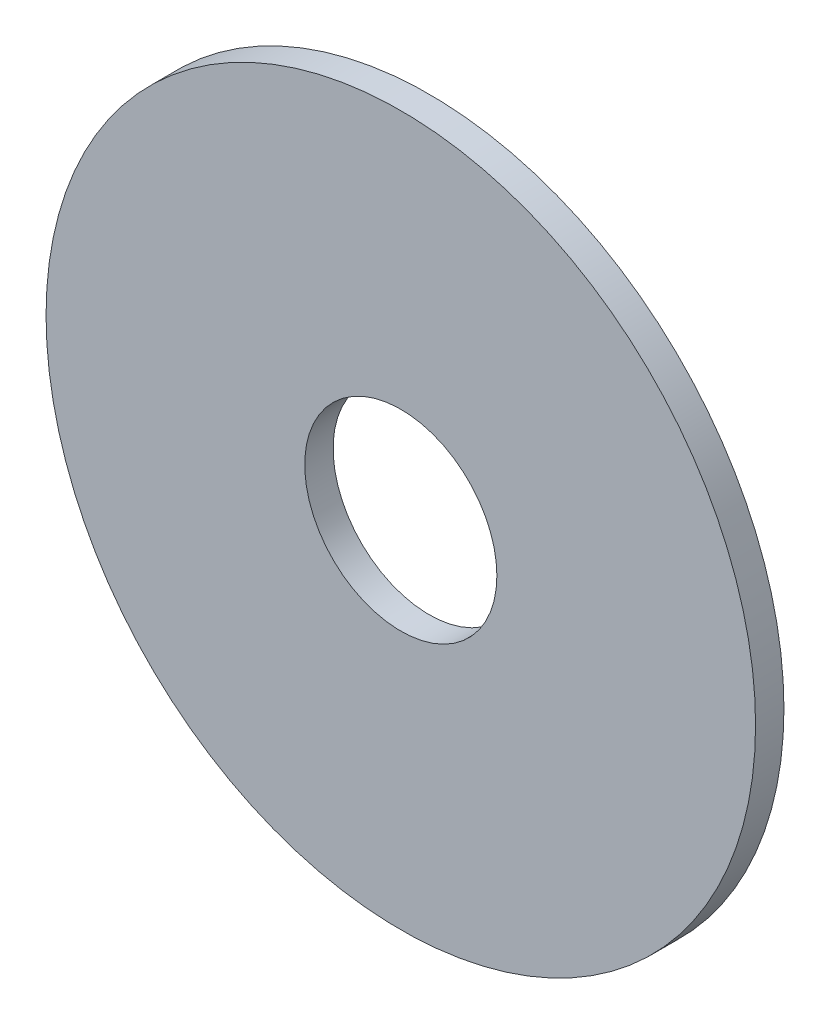
SolidWorks part; units mm, degrees
material "Plain Carbon Steel"
ref_plane "Front Plane" through (0, 0, 0) normal (0, 0, 1) x (1, 0, 0)
ref_plane "Top Plane" through (0, 0, 0) normal (0, 1, 0) x (1, 0, 0)
ref_plane "Right Plane" through (0, 0, 0) normal (1, 0, 0) x (0, 0, -1)
sketch "Sketch1" plane through (0, 0, 0) normal (0, 0, 1) x (1, 0, 0)
  circle A0 centre (0, 0) radius 2.5797
  circle A1 centre (0, 0) radius 9.525
  dimension "ID" = 5.1594
  dimension "OD" = 19.05
extrude "Extrude1" add sketch "Sketch1" against normal blind 0.762
